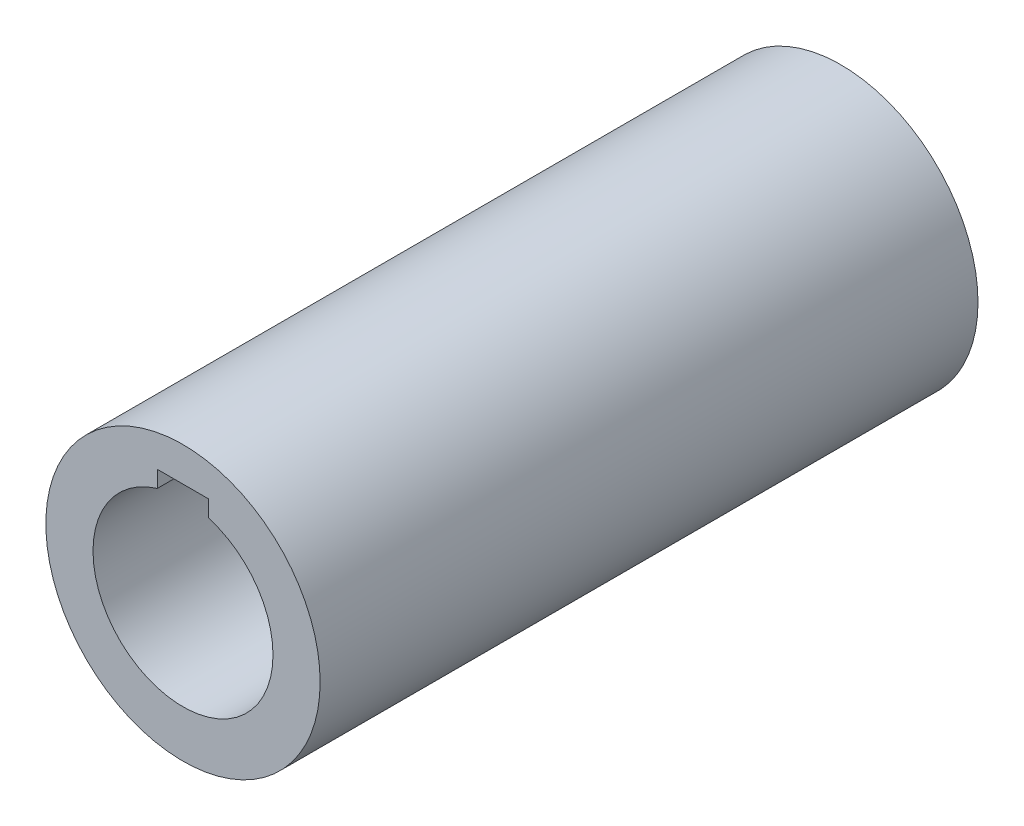
SolidWorks part; units mm, degrees
ref_plane "Front Plane" through (0, 0, 0) normal (0, 0, 1) x (1, 0, 0)
ref_plane "Top Plane" through (0, 0, 0) normal (0, 1, 0) x (1, 0, 0)
ref_plane "Right Plane" through (0, 0, 0) normal (1, 0, 0) x (0, 0, -1)
sketch "Sketch1" plane through (0, 0, 0) normal (0, 0, 1) x (1, 0, 0)
  circle A0 centre (0, 0) radius 21
  circle A1 centre (0, 0) radius 32
  dimension "D1" = 64
  dimension "D2" = 42
extrude "Boss-Extrude1" add sketch "Sketch1" along normal blind 153.5
sketch "Sketch2" plane through (0, 0, 153.5) normal (0, 0, 1) x (1, 0, 0)
  line L1 (-6, 24) -> (6, 24)
  line L2 (-6, 24) -> (-6, 20.1246)
  line L3 (-6, 20.1246) -> (6, 20.1246)
  line L4 (6, 24) -> (6, 20.1246)
  circle A0 centre (0, 0) radius 21 construction
  dimension "D1" = 12
  dimension "D2" = 24
extrude "Cut-Extrude1" cut sketch "Sketch2" against normal through all
